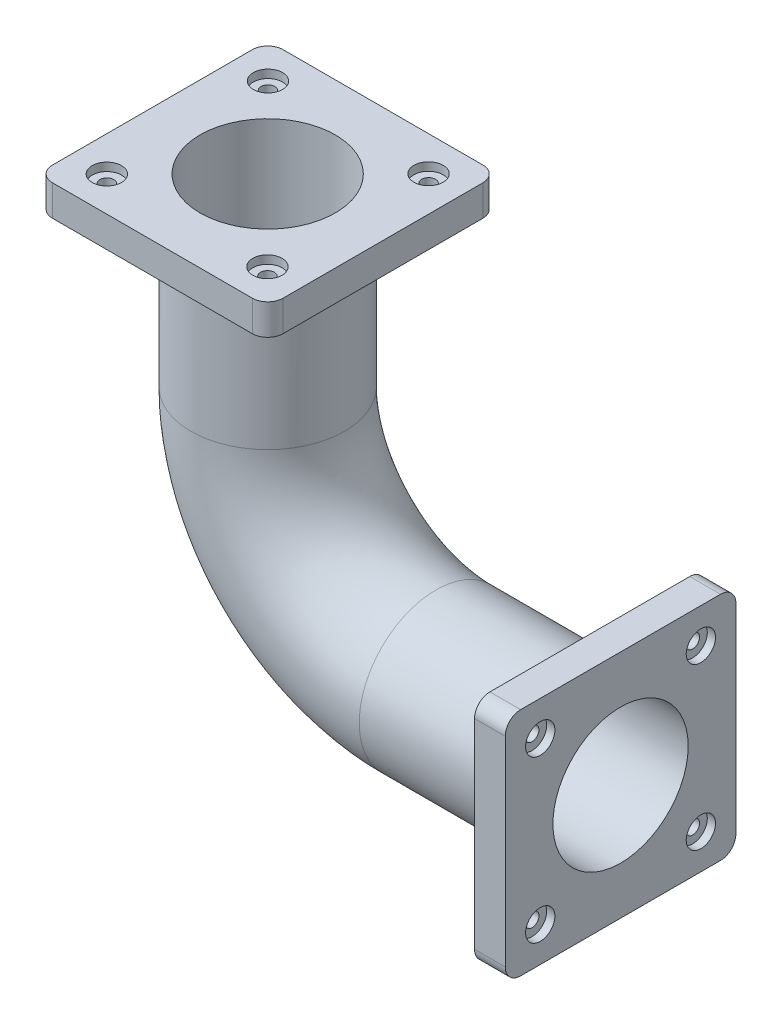
SolidWorks part; units mm, degrees
ref_plane "Front Plane" through (0, 0, 0) normal (0, 0, 1) x (1, 0, 0)
ref_plane "Top Plane" through (0, 0, 0) normal (0, 1, 0) x (1, 0, 0)
ref_plane "Right Plane" through (0, 0, 0) normal (1, 0, 0) x (0, 0, -1)
sketch "Sketch1" plane through (0, 0, 0) normal (0, 0, 1) x (1, 0, 0)
  line L0 (-55, 50) -> (-55, 0)
  line L1 (0, -55) -> (50, -55)
  arc A0 (-55, 0) -> (0, -55) centre (0, 0) ccw
  point P4 (0, 0)
  dimension "D2" = 55
  dimension "D1" = 50
ref_plane "Plane1" through (-55, 50, 0) normal (0, -1, 0) x (-1, 0, 0)
sketch "Sketch2" plane through (-55, 50, 0) normal (0, -1, 0) x (-1, 0, 0)
  circle A0 centre (-0.2336, 0) radius 25
  dimension "D1" = 50
sweep "Sweep1" add profiles "Sketch2" path "Sketch1"
shell "Shell2" thickness 3
sketch "Sketch3" plane through (0, 50, 0) normal (0, 1, 0) x (1, 0, 0)
  line L1 (-92.2664, 37.5) -> (-17.2664, 37.5)
  line L2 (-92.2664, 37.5) -> (-92.2664, -37.5)
  line L3 (-92.2664, -37.5) -> (-17.2664, -37.5)
  line L4 (-17.2664, 37.5) -> (-17.2664, -37.5)
  line L5 (-92.2664, 37.5) -> (-17.2664, -37.5) construction
  line L6 (-92.2664, -37.5) -> (-17.2664, 37.5) construction
  circle A0 centre (-54.7664, 0) radius 22
  point P0 (-54.7664, 0)
  dimension "D1" = 75
  dimension "D2" = 75
extrude "Boss-Extrude1" add sketch "Sketch3" along normal blind 10
fillet "Fillet1" radius 5 4 edges at (-92.2664, 55, 37.5) (-92.2664, 55, -37.5) (-17.2664, 55, -37.5) (-17.2664, 55, 37.5)
sketch "Sketch4" plane through (0, 60, 0) normal (0, 1, 0) x (1, 0, 0)
  line L0 (-54.7664, 0) -> (-54.7664, 50.0054) construction
  line L1 (-100.9813, 0) -> (-12.7078, 0) construction
  circle A0 centre (-80.884, 26.1978) radius 5
  circle A1 centre (-28.6488, 26.1978) radius 5
  circle A2 centre (-28.6488, -26.1978) radius 5
  circle A3 centre (-80.884, -26.1978) radius 5
  dimension "D1" = 10
hole_wizard "CBORE for #8 Binding Head Machine Screw1" positions "3DSketch1" profile "Sketch5" counterbore size "#8" standard "ANSI Inch"
sketch3d "3DSketch1"
  point P0 (-80.884, 60, -26.1978)
  point P3 (-28.6488, 60, -26.1978)
  point P6 (-80.884, 60, 26.1978)
  point P9 (-28.6488, 60, 26.1978)
sketch "Sketch5" plane through (-80.884, 60, -26.1978) normal (1, 0, 0) x (0, 0, 1)
  line L0 (0, 0) -> (0, 21.3507)
  line L1 (0, 21.3507) -> (2.2479, 20)
  line L2 (2.2479, 20) -> (2.2479, 2.667)
  line L3 (2.2479, 2.667) -> (4.7625, 2.667)
  line L4 (4.7625, 2.667) -> (4.7625, 0)
  line L5 (4.7625, 0) -> (0, 0)
  line L10 (0, 21.3507) -> (-2.2479, 20) construction
  line L11 (0, -6.35) -> (0, 107.95) construction
  dimension "Hole Dia." = 4.4958
  dimension "Hole Depth" = 20
  dimension "C'Bore Dia." = 9.525
  dimension "C'Bore Depth" = 2.667
  dimension "Drill Angle" = 118
sketch "Sketch6" plane through (50, 0, 0) normal (1, 0, 0) x (0, 0, -1)
  line L0 (0, -54.7664) -> (0, 12.2411) construction
  line L1 (-37.5, -17.2664) -> (37.5, -17.2664)
  line L2 (-37.5, -17.2664) -> (-37.5, -92.2664)
  line L3 (-37.5, -92.2664) -> (37.5, -92.2664)
  line L4 (37.5, -17.2664) -> (37.5, -92.2664)
  line L5 (-37.5, -17.2664) -> (37.5, -92.2664) construction
  line L6 (-37.5, -92.2664) -> (37.5, -17.2664) construction
  line L7 (-60.3059, -54.7664) -> (56.3722, -54.7664) construction
  circle A0 centre (0, -54.7664) radius 22
  point P0 (0, -54.7664)
  point P8 (-26.12, -28.5664)
  point P13 (26.12, -28.5664)
  point P14 (26.12, -80.9664)
  point P15 (-26.12, -80.9664)
  dimension "D1" = 75
  dimension "D2" = 75
  dimension "D3" = 26.2
  dimension "D4" = 26.12
extrude "Boss-Extrude2" add sketch "Sketch6" along normal blind 10
fillet "Fillet2" radius 5 4 edges at (55, -17.2664, 37.5) (55, -17.2664, -37.5) (55, -92.2664, -37.5) (55, -92.2664, 37.5)
sketch "Sketch10" plane through (60, 0, 0) normal (1, 0, 0) x (0, 0, -1)
  line L0 (0, -32.7664) -> (0, -76.7664) construction
  line L1 (-47.9926, -54.7664) -> (66.674, -54.7664) construction
  circle A0 centre (0, -54.7664) radius 22 construction
  circle A1 centre (0, -54.7664) radius 22 construction
  point P9 (-26.12, -28.5664)
  point P10 (0, -54.7664)
  point P11 (26.12, -28.5664)
  point P12 (26.12, -80.9664)
  point P13 (-26.12, -80.9664)
  dimension "D1" = 26.2
  dimension "D2" = 26.12
hole_wizard "CBORE for #8 Binding Head Machine Screw2" positions "Sketch10" profile "Sketch11" counterbore size "#8" standard "ANSI Inch"
sketch "Sketch11" plane through (60, -80.9664, 26.12) normal (0, 1, 0) x (0, 0, -1)
  line L0 (0, 0) -> (0, 21.3507)
  line L1 (0, 21.3507) -> (2.2479, 20)
  line L2 (2.2479, 20) -> (2.2479, 2.667)
  line L3 (2.2479, 2.667) -> (4.7625, 2.667)
  line L4 (4.7625, 2.667) -> (4.7625, 0)
  line L5 (4.7625, 0) -> (0, 0)
  line L10 (0, 21.3507) -> (-2.2479, 20) construction
  line L11 (0, -6.35) -> (0, 107.95) construction
  dimension "Hole Dia." = 4.4958
  dimension "Hole Depth" = 20
  dimension "C'Bore Dia." = 9.525
  dimension "C'Bore Depth" = 2.667
  dimension "Drill Angle" = 118
